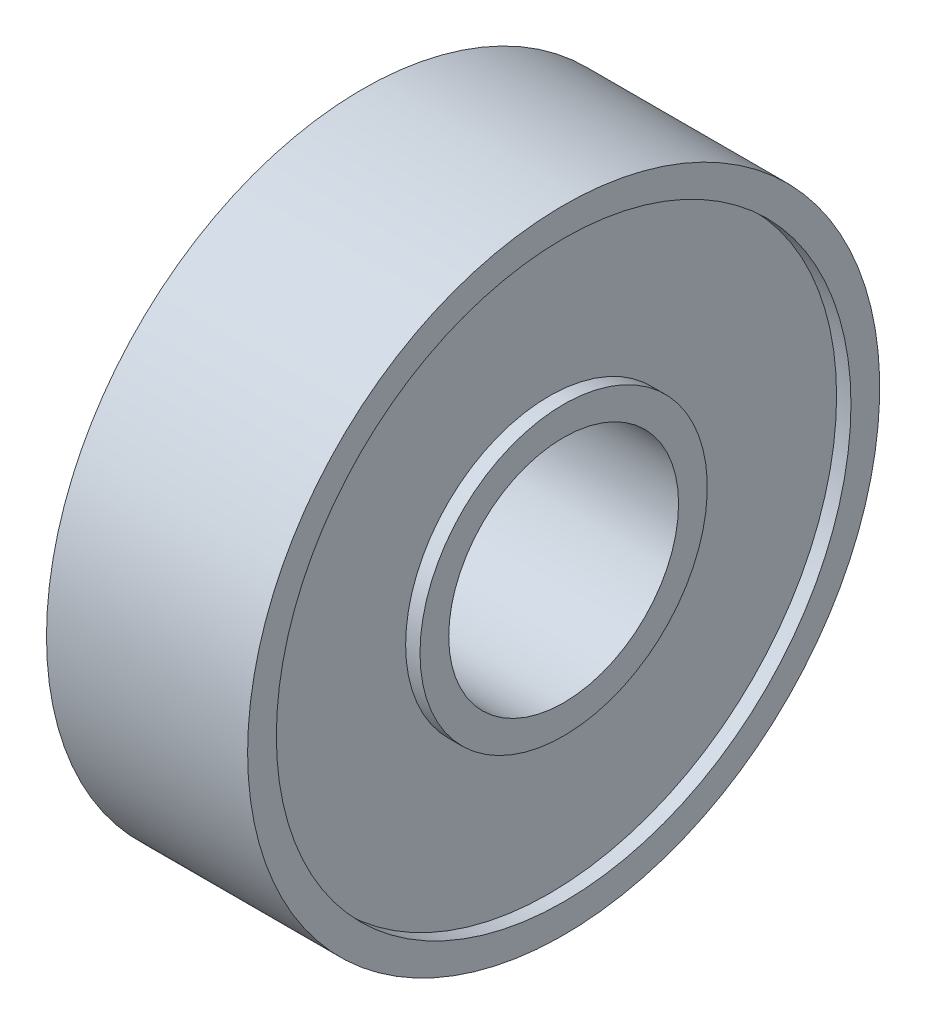
SolidWorks part; units mm, degrees
material "AISI 304"
ref_plane "Front Plane" through (0, 0, 0) normal (0, 0, 1) x (1, 0, 0)
ref_plane "Top Plane" through (0, 0, 0) normal (0, 1, 0) x (1, 0, 0)
ref_plane "Right Plane" through (0, 0, 0) normal (1, 0, 0) x (0, 0, -1)
sketch "Sketch1" plane through (0, 0, 0) normal (0, 0, 1) x (1, 0, 0)
  line L0 (0, 4) -> (0, 0) construction
  line L1 (-3.5, 11) -> (3.5, 11)
  line L2 (-3.5, 11) -> (-3.5, 10)
  line L3 (-3.5, 4) -> (3.5, 4)
  line L4 (3.5, 11) -> (3.5, 10)
  line L5 (-3.3544, 0) -> (4.1757, 0) construction
  line L6 (3.5, 5) -> (3.5, 4)
  line L7 (-3.5, 10) -> (-3, 10)
  line L9 (-3.5, 5) -> (-3, 5)
  line L10 (-3, 10) -> (-3, 5)
  line L11 (3.5, 5) -> (3, 5)
  line L12 (-3.5, 5) -> (-3.5, 4)
  line L13 (3.5, 10) -> (3, 10)
  line L14 (3, 5) -> (3, 10)
  dimension "D1" = 8
  dimension "D2" = 22
  dimension "D3" = 7
  dimension "D4" = 0.5
  dimension "D5" = 10
  dimension "D6" = 20
revolve "Revolve1" add sketch "Sketch1" angle 360 about L5
